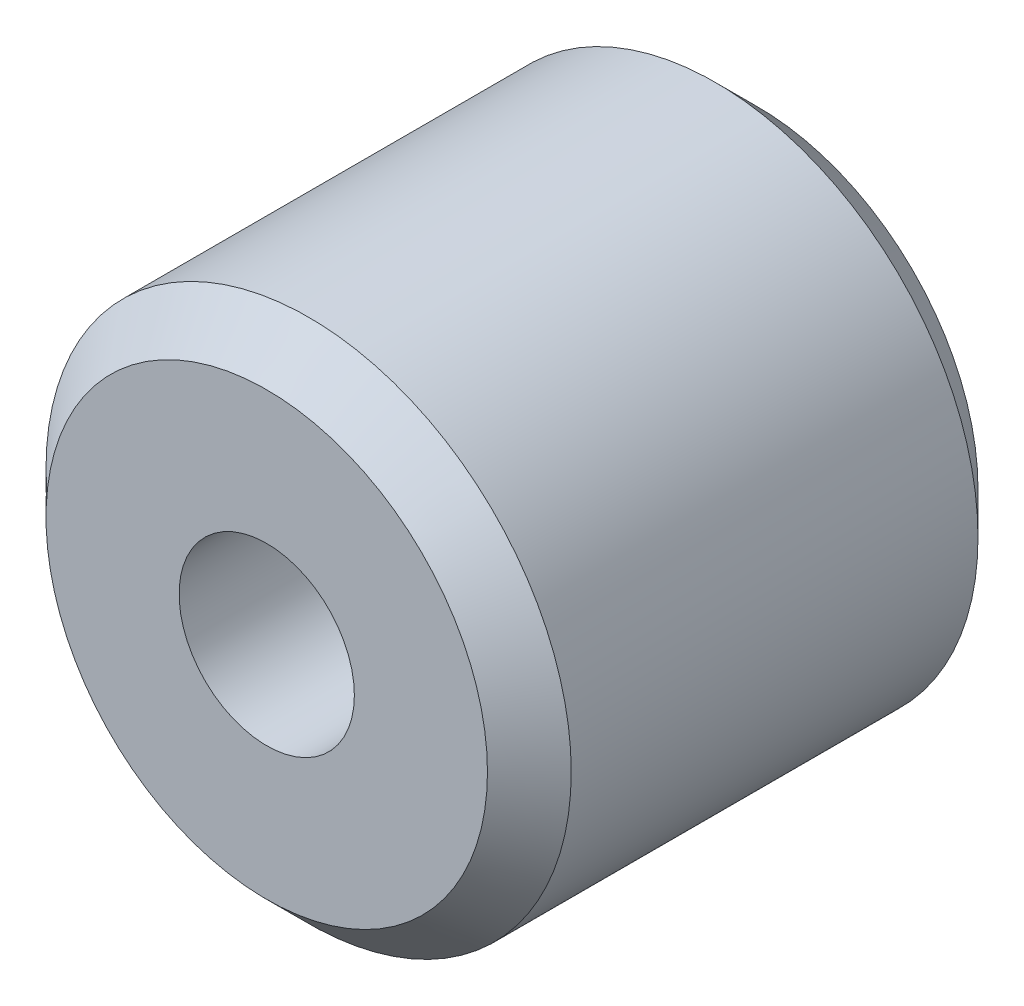
SolidWorks part; units mm, degrees
ref_plane "Plan de face" through (0, 0, 0) normal (0, 0, 1) x (1, 0, 0)
ref_plane "Plan de dessus" through (0, 0, 0) normal (0, 1, 0) x (1, 0, 0)
ref_plane "Plan de droite" through (0, 0, 0) normal (1, 0, 0) x (0, 0, -1)
sketch "Esquisse1" plane through (0, 0, 0) normal (0, 0, 1) x (1, 0, 0)
  circle A0 centre (0, 0) radius 1.59
  circle A1 centre (0, 0) radius 4.765
  dimension "D1" = 3.18
  dimension "D2" = 9.53
extrude "Boss.-Extru.1" add sketch "Esquisse1" along normal mid plane 8.9
chamfer "Chanfrein1" distance 0.76 angle 45 2 edges at (4.765, 0, -4.45) (4.765, 0, 4.45)
